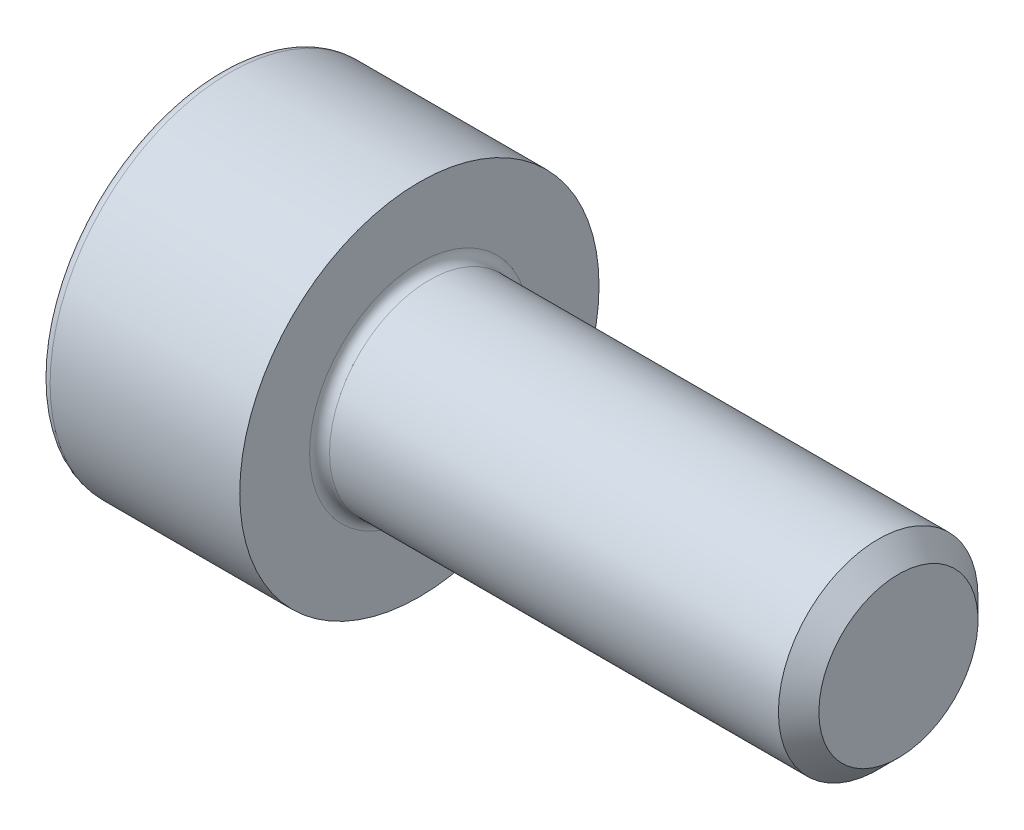
SolidWorks part; units mm, degrees
ref_plane "Front" through (0, 0, 0) normal (0, 0, 1) x (1, 0, 0)
ref_plane "Top" through (0, 0, 0) normal (0, 1, 0) x (1, 0, 0)
ref_plane "Right" through (0, 0, 0) normal (1, 0, 0) x (0, 0, -1)
sketch "Sketch1" plane through (0, 0, 0) normal (0, 0, 1) x (1, 0, 0)
  line L0 (5.7465, 1.25) -> (0.125, 1.25)
  line L1 (-2.5, 2.125) -> (-2.5, 0)
  line L2 (0, 2.25) -> (-2.375, 2.25)
  line L3 (0, 1.375) -> (0, 2.25)
  line L4 (6, 0.9965) -> (6, 0)
  line L5 (6, 0.9965) -> (5.7465, 1.25)
  line L6 (-2.5, 0) -> (0, 0) construction
  line L7 (-2.5, 0) -> (6, 0)
  arc A0 (-2.375, 2.25) -> (-2.5, 2.125) centre (-2.375, 2.125) ccw
  arc A1 (0, 1.375) -> (0.125, 1.25) centre (0.125, 1.375) ccw
  point P12 (0, 1.8125)
  dimension "D5" = 0.125
  dimension "D1" = 2.5
  dimension "D2" = 4.5
  dimension "D3" = 135
  dimension "D4" = 0.3585
  dimension "D6" = 6
  dimension "D7" = 2.5
revolve "Revolve1" add sketch "Sketch1" angle 360 about L7
sketch "Sketch2" plane through (-2.5, 0, 0) normal (-1, 0, 0) x (0, 0, 1)
  line L7 (1.025, 0.5918) -> (0, 1.1836)
  line L8 (0, 1.1836) -> (-1.025, 0.5918)
  line L9 (-1.025, 0.5918) -> (-1.025, -0.5918)
  line L10 (-1.025, -0.5918) -> (0, -1.1836)
  line L11 (0, -1.1836) -> (1.025, -0.5918)
  line L12 (1.025, -0.5918) -> (1.025, 0.5918)
  circle A0 centre (0, 0) radius 1.025 construction
  dimension "D1" = 2.05
extrude "Cut-Extrude1" cut sketch "Sketch2" against normal blind 1.1
